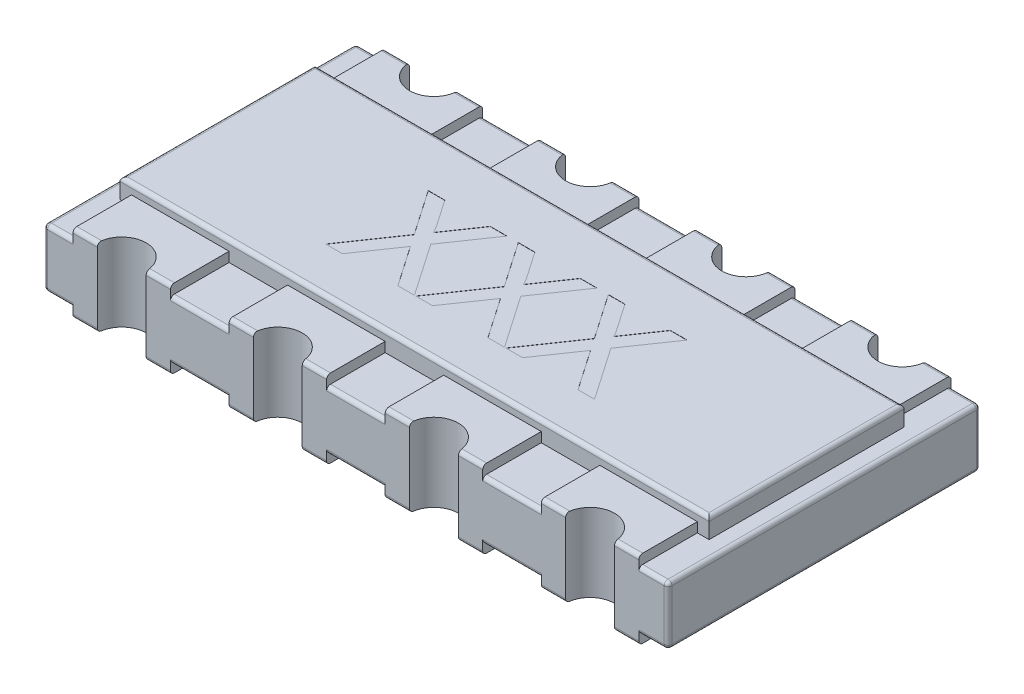
SolidWorks part; units mm, degrees
ref_plane "Спереди" through (0, 0, 0) normal (0, 0, 1) x (1, 0, 0)
ref_plane "Сверху" through (0, 0, 0) normal (0, 1, 0) x (1, 0, 0)
ref_plane "Справа" through (0, 0, 0) normal (1, 0, 0) x (0, 0, -1)
sketch "Sketch1" plane through (0, 0, 0) normal (0, 1, 0) x (1, 0, 0)
  line L0 (0, 0) -> (0, 0.75) construction
  line L1 (-1.33, -0.8) -> (-1.6, -0.8)
  line L2 (1.6, -0.8) -> (1.6, 0.8)
  line L3 (1.6, 0.8) -> (1.33, 0.8)
  line L4 (-1.6, -0.8) -> (-1.6, 0.8)
  line L5 (1.6, -0.8) -> (-1.6, 0.8) construction
  line L6 (1.6, 0.8) -> (-1.6, -0.8) construction
  line L7 (0, 0) -> (1.6, 0) construction
  line L8 (-0.53, -0.8) -> (-1.07, -0.8)
  line L9 (0.27, -0.8) -> (-0.27, -0.8)
  line L10 (1.07, -0.8) -> (0.53, -0.8)
  line L11 (1.6, -0.8) -> (1.33, -0.8)
  line L12 (1.07, 0.8) -> (0.53, 0.8)
  line L13 (0.27, 0.8) -> (-0.27, 0.8)
  line L14 (-0.53, 0.8) -> (-1.07, 0.8)
  line L15 (-1.33, 0.8) -> (-1.6, 0.8)
  arc A0 (-1.33, 0.8) -> (-1.07, 0.8) centre (-1.2, 0.8) ccw
  arc A1 (-0.53, 0.8) -> (-0.27, 0.8) centre (-0.4, 0.8) ccw
  arc A2 (0.27, 0.8) -> (0.53, 0.8) centre (0.4, 0.8) ccw
  arc A3 (1.07, 0.8) -> (1.33, 0.8) centre (1.2, 0.8) ccw
  arc A4 (1.07, -0.8) -> (1.33, -0.8) centre (1.2, -0.8) cw
  arc A5 (0.27, -0.8) -> (0.53, -0.8) centre (0.4, -0.8) cw
  arc A6 (-0.53, -0.8) -> (-0.27, -0.8) centre (-0.4, -0.8) cw
  arc A7 (-1.33, -0.8) -> (-1.07, -0.8) centre (-1.2, -0.8) cw
  arc A8 (-0.3169, -0.8) -> (-0.4831, -0.8) centre (-0.4, -0.7) ccw [skipped]
  arc A9 (0.4831, -0.8) -> (0.3169, -0.8) centre (0.4, -0.7) ccw [skipped]
  arc A10 (1.2831, -0.8) -> (1.1169, -0.8) centre (1.2, -0.7) ccw [skipped]
  arc A11 (-1.1169, -0.8) -> (-1.2831, -0.8) centre (-1.2, -0.7) ccw [skipped]
  point P0 (0, 0)
  dimension "D3" = 4
  dimension "D1" = 3.2
  dimension "D2" = 1.6
  dimension "D4" = 2
extrude "Boss-Extrude1" add sketch "Sketch1" along normal blind 0.3 from offset 0.05
fillet "Fillet1" radius 0.02 44 edges at (-1.6, 0.2, -0.8) (1.6, 0.2, -0.8) (-1.6, 0.05, 0) (1.6, 0.05, 0) (1.465, 0.05, -0.8) (1.2, 0.05, -0.67) (0.8, 0.05, -0.8) (0.4, 0.05, -0.67) (0, 0.05, -0.8) (-0.4, 0.05, -0.67) (-0.8, 0.05, -0.8) (-1.2, 0.05, -0.67) (-1.465, 0.05, -0.8) (-1.2, 0.35, -0.67) (-0.8, 0.35, -0.8) (-0.4, 0.35, -0.67) (0, 0.35, -0.8) (0.4, 0.35, -0.67) (0.8, 0.35, -0.8) (1.2, 0.35, -0.67) (1.465, 0.35, -0.8) (1.6, 0.35, 0) (-1.6, 0.35, 0) (-1.465, 0.35, -0.8) (-1.6, 0.2, 0.8) (1.6, 0.2, 0.8) (-1.465, 0.05, 0.8) (-1.2, 0.05, 0.67) (-0.8, 0.05, 0.8) (-0.4, 0.05, 0.67) (0, 0.05, 0.8) (0.4, 0.05, 0.67) (0.8, 0.05, 0.8) (1.2, 0.05, 0.67) (1.465, 0.05, 0.8) (1.465, 0.35, 0.8) (1.2, 0.35, 0.67) (0.8, 0.35, 0.8) (0.4, 0.35, 0.67) (0, 0.35, 0.8) (-0.4, 0.35, 0.67) (-0.8, 0.35, 0.8) (-1.2, 0.35, 0.67) (-1.465, 0.35, 0.8)
sketch "Sketch2" plane through (0, 0, 0) normal (0, 1, 0) x (1, 0, 0)
  line L0 (-1.075, 0.8) -> (-0.95, 0.8)
  line L1 (-1.45, 0.5) -> (-0.95, 0.5)
  line L2 (-1.45, 0.5) -> (-1.45, 0.8)
  line L3 (-1.45, 0.8) -> (-1.325, 0.8)
  line L4 (-0.95, 0.5) -> (-0.95, 0.8)
  line L6 (-0.275, 0.8) -> (-0.15, 0.8)
  line L7 (-0.65, 0.5) -> (-0.15, 0.5)
  line L8 (-0.65, 0.5) -> (-0.65, 0.8)
  line L9 (-0.65, 0.8) -> (-0.525, 0.8)
  line L10 (-0.15, 0.5) -> (-0.15, 0.8)
  line L11 (0.525, 0.8) -> (0.65, 0.8)
  line L12 (0.15, 0.5) -> (0.65, 0.5)
  line L13 (0.15, 0.5) -> (0.15, 0.8)
  line L14 (0.15, 0.8) -> (0.275, 0.8)
  line L15 (0.65, 0.5) -> (0.65, 0.8)
  line L16 (1.325, 0.8) -> (1.45, 0.8)
  line L17 (0.95, 0.5) -> (1.45, 0.5)
  line L18 (0.95, 0.5) -> (0.95, 0.8)
  line L19 (0.95, 0.8) -> (1.075, 0.8)
  line L20 (1.45, 0.5) -> (1.45, 0.8)
  line L36 (-1.075, -0.8) -> (-0.95, -0.8)
  line L41 (-0.95, -0.5) -> (-0.95, -0.8)
  line L42 (-1.45, -0.8) -> (-1.325, -0.8)
  line L43 (-1.45, -0.5) -> (-1.45, -0.8)
  line L44 (-1.45, -0.5) -> (-0.95, -0.5)
  line L45 (1.45, -0.5) -> (1.45, -0.8)
  line L46 (0.95, -0.8) -> (1.075, -0.8)
  line L47 (0.95, -0.5) -> (0.95, -0.8)
  line L48 (0.95, -0.5) -> (1.45, -0.5)
  line L49 (1.325, -0.8) -> (1.45, -0.8)
  line L50 (0.65, -0.5) -> (0.65, -0.8)
  line L51 (0.15, -0.8) -> (0.275, -0.8)
  line L52 (0.15, -0.5) -> (0.15, -0.8)
  line L53 (0.15, -0.5) -> (0.65, -0.5)
  line L54 (0.525, -0.8) -> (0.65, -0.8)
  line L55 (-0.15, -0.5) -> (-0.15, -0.8)
  line L56 (-0.65, -0.8) -> (-0.525, -0.8)
  line L57 (-0.65, -0.5) -> (-0.65, -0.8)
  line L58 (-0.65, -0.5) -> (-0.15, -0.5)
  line L59 (-0.275, -0.8) -> (-0.15, -0.8)
  line L60 (-0.95, -1.1) -> (-0.95, -0.8) [skipped]
  line L61 (-1.45, -0.8) -> (-1.325, -0.8) [skipped]
  line L62 (-1.45, -1.1) -> (-1.45, -0.8) [skipped]
  line L63 (-1.45, -1.1) -> (-0.95, -1.1) [skipped]
  line L64 (1.45, -1.1) -> (1.45, -0.8) [skipped]
  line L65 (0.95, -0.8) -> (1.075, -0.8) [skipped]
  line L66 (0.95, -1.1) -> (0.95, -0.8) [skipped]
  line L67 (0.95, -1.1) -> (1.45, -1.1) [skipped]
  line L68 (1.325, -0.8) -> (1.45, -0.8) [skipped]
  line L69 (0.65, -1.1) -> (0.65, -0.8) [skipped]
  line L70 (0.15, -0.8) -> (0.275, -0.8) [skipped]
  line L71 (0.15, -1.1) -> (0.15, -0.8) [skipped]
  line L72 (0.15, -1.1) -> (0.65, -1.1) [skipped]
  line L73 (0.525, -0.8) -> (0.65, -0.8) [skipped]
  line L74 (-0.15, -1.1) -> (-0.15, -0.8) [skipped]
  line L75 (-0.65, -0.8) -> (-0.525, -0.8) [skipped]
  line L76 (-0.65, -1.1) -> (-0.65, -0.8) [skipped]
  line L77 (-0.65, -1.1) -> (-0.15, -1.1) [skipped]
  line L78 (-0.275, -0.8) -> (-0.15, -0.8) [skipped]
  arc A0 (-1.325, 0.8) -> (-1.075, 0.8) centre (-1.2, 0.8) ccw
  arc A1 (-0.525, 0.8) -> (-0.275, 0.8) centre (-0.4, 0.8) ccw
  arc A2 (0.275, 0.8) -> (0.525, 0.8) centre (0.4, 0.8) ccw
  arc A3 (1.075, 0.8) -> (1.325, 0.8) centre (1.2, 0.8) ccw
  arc A8 (-1.325, -0.8) -> (-1.075, -0.8) centre (-1.2, -0.8) cw
  arc A9 (1.075, -0.8) -> (1.325, -0.8) centre (1.2, -0.8) cw
  arc A10 (0.275, -0.8) -> (0.525, -0.8) centre (0.4, -0.8) cw
  arc A11 (-0.525, -0.8) -> (-0.275, -0.8) centre (-0.4, -0.8) cw
  arc A12 (-1.325, -0.8) -> (-1.075, -0.8) centre (-1.2, -0.8) ccw [skipped]
  arc A13 (1.075, -0.8) -> (1.325, -0.8) centre (1.2, -0.8) ccw [skipped]
  arc A14 (0.275, -0.8) -> (0.525, -0.8) centre (0.4, -0.8) ccw [skipped]
  arc A15 (-0.525, -0.8) -> (-0.275, -0.8) centre (-0.4, -0.8) ccw [skipped]
  dimension "D1" = 0.5
  dimension "D2" = 0.3
  dimension "D3" = 0.8
  dimension "D4" = 1.2
  dimension "D5" = 4
  dimension "D6" = 2
extrude "Boss-Extrude2" add sketch "Sketch2" along normal blind 0.4 separate body
sketch "Sketch3" plane through (0, 0.35, 0) normal (0, 1, 0) x (1, 0, 0)
  line L0 (1.45, 0.5) -> (1.51, 0.5) construction
  line L1 (-1.51, -0.5) -> (1.51, -0.5)
  line L2 (-1.51, -0.5) -> (-1.51, 0.5)
  line L3 (-1.51, 0.5) -> (1.51, 0.5)
  line L4 (1.51, -0.5) -> (1.51, 0.5)
  line L5 (-1.51, -0.5) -> (1.51, 0.5) construction
  line L6 (-1.51, 0.5) -> (1.51, -0.5) construction
  point P0 (0, 0)
extrude "Boss-Extrude3" add sketch "Sketch3" along normal blind 0.1
fillet "Fillet2" radius 0.02 44 edges at (0, 0.45, -0.5) (1.51, 0.45, 0) (0, 0.45, 0.5) (-1.51, 0.45, 0) (-1.2, 0, 0.5) (-0.4, 0, 0.5) (0.4, 0, 0.5) (1.2, 0, 0.5) (1.2, 0, -0.5) (0.4, 0, -0.5) (-0.4, 0, -0.5) (-1.2, 0, -0.5) (-1.3875, 0, -0.8) (-1.0125, 0, -0.8) (-0.5875, 0, -0.8) (-0.2125, 0, -0.8) (0.2125, 0, -0.8) (0.5875, 0, -0.8) (1.0125, 0, -0.8) (1.3875, 0, -0.8) (1.3875, 0, 0.8) (1.0125, 0, 0.8) (0.5875, 0, 0.8) (0.2125, 0, 0.8) (-0.2125, 0, 0.8) (-0.5875, 0, 0.8) (-1.0125, 0, 0.8) (-1.3875, 0, 0.8) (-1.3875, 0.4, -0.8) (-1.0125, 0.4, -0.8) (-0.5875, 0.4, -0.8) (-0.2125, 0.4, -0.8) (0.2125, 0.4, -0.8) (0.5875, 0.4, -0.8) (1.0125, 0.4, -0.8) (1.3875, 0.4, -0.8) (1.3875, 0.4, 0.8) (1.0125, 0.4, 0.8) (0.5875, 0.4, 0.8) (0.2125, 0.4, 0.8) (-0.2125, 0.4, 0.8) (-0.5875, 0.4, 0.8) (-1.0125, 0.4, 0.8) (-1.3875, 0.4, 0.8)
sketch "Sketch4" plane through (0, 0.45, 0) normal (0, 1, 0) x (1, 0, 0)
  text T0 "XXX" font "Arial" height 0.5
extrude "Cut-Extrude1" cut sketch "Sketch4" against normal blind 0.001
